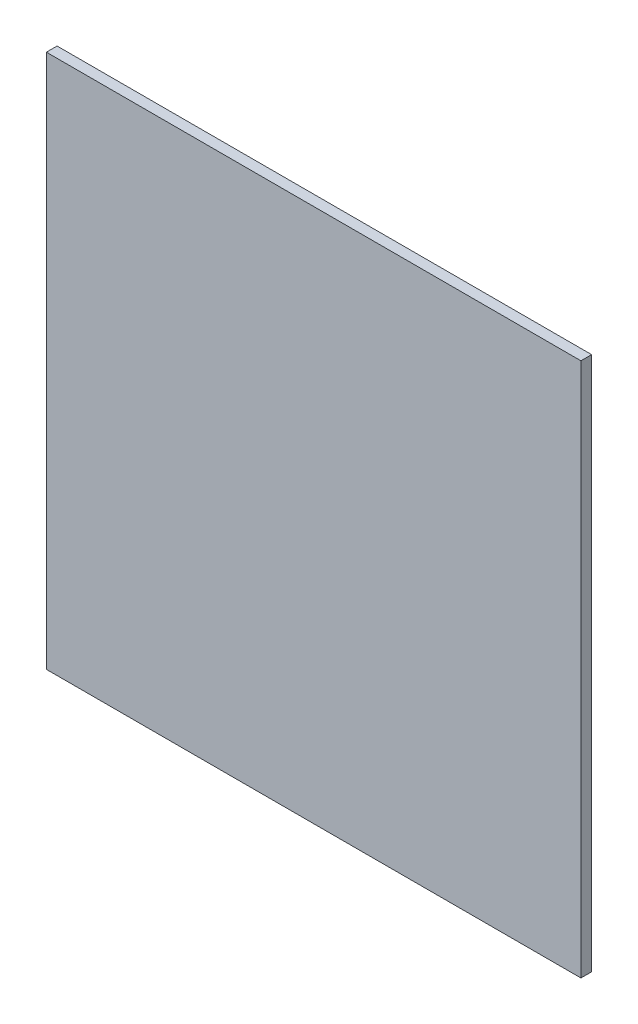
SolidWorks part; units mm, degrees
ref_plane "Płaszczyzna przednia" through (0, 0, 0) normal (0, 0, 1) x (1, 0, 0)
ref_plane "Płaszczyzna górna" through (0, 0, 0) normal (0, 1, 0) x (1, 0, 0)
ref_plane "Płaszczyzna prawa" through (0, 0, 0) normal (1, 0, 0) x (0, 0, -1)
sketch "Szkic1" plane through (0, 0, 0) normal (0, 0, 1) x (1, 0, 0)
  line L0 (0, 0) -> (100, 0)
  line L1 (0, 0) -> (-100, 0)
  line L2 (0, 0) -> (0, 100)
  line L3 (0, 0) -> (0, -100)
  line L4 (0, 100) -> (100, 100)
  line L5 (100, 100) -> (100, 0)
  line L6 (100, -100) -> (0, -100)
  line L7 (100, 0) -> (100, -100)
  line L8 (0, 100) -> (-100, 100)
  line L9 (-100, 100) -> (-100, 0)
  line L10 (-100, -100) -> (-100, 0)
  line L11 (0, -100) -> (-100, -100)
  dimension "D1" = 100
  dimension "D2" = 100
  dimension "D3" = 100
  dimension "D4" = 100
  dimension "D5" = 100
  dimension "D6" = 100
  dimension "D7" = 100
  dimension "D8" = 100
  dimension "D9" = 100
  dimension "D10" = 100
  dimension "D11" = 100
extrude "Dodanie-wyciągnięcie1" add sketch "Szkic1" along normal blind 4 contours L8 L9 L1 L2 | L5 L4 L2 L0 | L7 L0 L3 L6 | L11 L3 L1 L10
